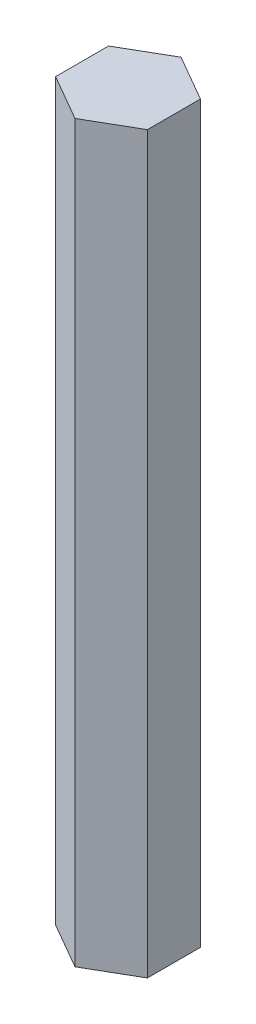
SolidWorks part; units mm, degrees
ref_plane "Front Plane" through (0, 0, 0) normal (0, 0, 1) x (1, 0, 0)
ref_plane "Top Plane" through (0, 0, 0) normal (0, 1, 0) x (1, 0, 0)
ref_plane "Right Plane" through (0, 0, 0) normal (1, 0, 0) x (0, 0, -1)
sketch "Sketch1" plane through (0, 0, 0) normal (0, 1, 0) x (1, 0, 0)
  line L1 (0, 5.7735) -> (-5, 2.8868)
  line L2 (-5, 2.8868) -> (-5, -2.8868)
  line L3 (-5, -2.8868) -> (0, -5.7735)
  line L4 (0, -5.7735) -> (5, -2.8868)
  line L5 (5, -2.8868) -> (5, 2.8868)
  line L6 (5, 2.8868) -> (0, 5.7735)
  circle A0 centre (0, 0) radius 5 construction
  dimension "D1" = 10
extrude "Boss-Extrude1" add sketch "Sketch1" along normal blind 80
sketch "Sketch2" plane through (0, 0, 0) normal (0, -1, 0) x (1, 0, 0)
  circle A0 centre (0, 0) radius 3
  dimension "D1" = 6
extrude "Cut-Extrude1" cut sketch "Sketch2" against normal blind 5
